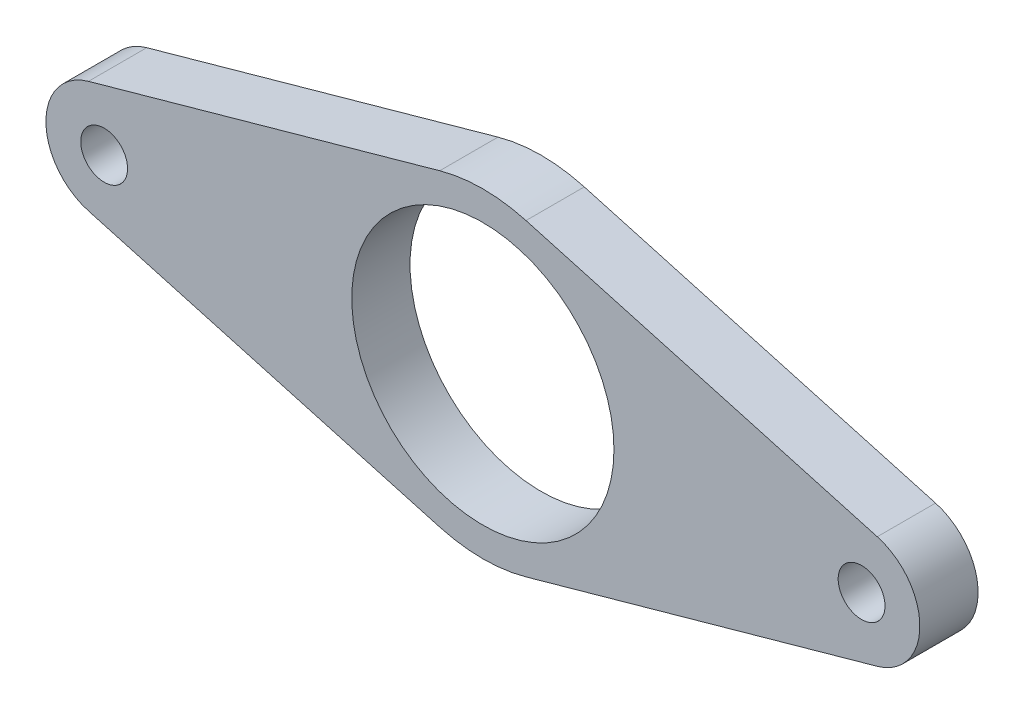
SolidWorks part; units mm, degrees
material "6061-T6 (SS)"
ref_plane "Front Plane" through (0, 0, 0) normal (0, 0, 1) x (1, 0, 0)
ref_plane "Top Plane" through (0, 0, 0) normal (0, 1, 0) x (1, 0, 0)
ref_plane "Right Plane" through (0, 0, 0) normal (1, 0, 0) x (0, 0, -1)
sketch "Sketch1" plane through (0, 0, 0) normal (0, 0, 1) x (1, 0, 0)
  line L0 (-42.9846, 6.1155) -> (-4.7014, 16.8177)
  line L1 (-42.9846, -6.1155) -> (-4.7014, -16.8177)
  line L2 (42.9846, -6.1155) -> (4.7014, -16.8177)
  line L3 (42.9846, 6.1155) -> (4.7014, 16.8177)
  arc A0 (-4.7014, -16.8177) -> (4.7014, -16.8177) centre (0, 0) ccw
  circle A1 centre (-41.275, 0) radius 2.5527
  circle A2 centre (41.275, 0) radius 2.5527
  circle A3 centre (0, 0) radius 14.2875
  arc A4 (-42.9846, 6.1155) -> (-42.9846, -6.1155) centre (-41.275, 0) ccw
  arc A5 (42.9846, 6.1155) -> (42.9846, -6.1155) centre (41.275, 0) cw
  arc A6 (4.7014, 16.8177) -> (-4.7014, 16.8177) centre (0, 0) ccw
  dimension "D1" = 28.575
  dimension "D2" = 5.1054
  dimension "D3" = 34.925
  dimension ".25" = 6.35
  dimension "D4" = 41.275
  dimension "D5" = 41.275
extrude "Boss-Extrude1" add sketch "Sketch1" along normal blind 6.35 contours L3 A6 L0 A4 L1 A0 L2 A5 A1 A2 A3
